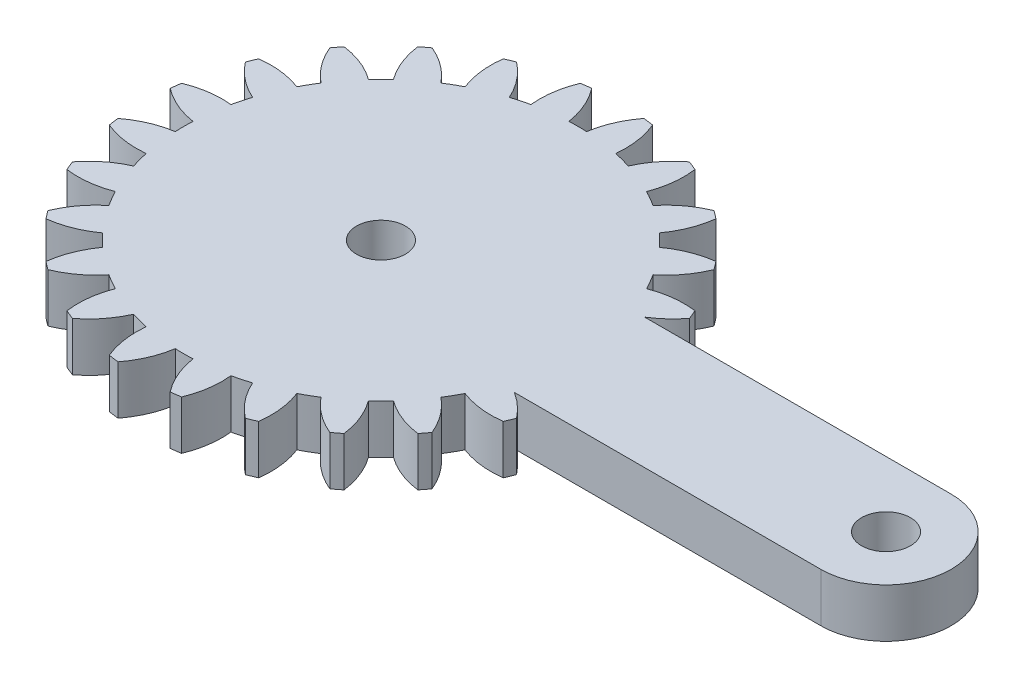
SolidWorks part; units mm, degrees
ref_plane "Front Plane" through (0, 0, 0) normal (0, 0, 1) x (1, 0, 0)
ref_plane "Top Plane" through (0, 0, 0) normal (0, 1, 0) x (1, 0, 0)
ref_plane "Right Plane" through (0, 0, 0) normal (1, 0, 0) x (0, 0, -1)
sketch "Sketch1" plane through (0, 0, 0) normal (0, 1, 0) x (1, 0, 0)
  line L0 (20.8937, 4) -> (2.0816, 4)
  line L1 (2.0816, -4) -> (20.8937, -4)
  line L2 (20.8937, 0) -> (-10.1063, 0) construction
  arc A0 (2.0816, 4) -> (3.5217, 5.3071) centre (-0.7683, 8.5867) ccw
  arc A1 (3.5217, 5.3071) -> (3.2829, 5.8838) centre (-10.1063, 0) ccw
  arc A2 (3.2829, 5.8838) -> (0.6271, 5.5703) centre (2.5684, 0.5313) ccw
  arc A3 (0.6271, 5.5703) -> (0.0844, 6.5103) centre (-10.1063, 0) ccw
  arc A4 (0.0844, 6.5103) -> (1.6838, 8.6535) centre (-3.3089, 10.711) ccw
  arc A5 (1.6838, 8.6535) -> (1.3038, 9.1487) centre (-10.1063, 0) ccw
  arc A6 (1.3038, 9.1487) -> (-1.1803, 8.1585) centre (1.999, 3.7936) ccw
  arc A7 (-1.1803, 8.1585) -> (-1.9479, 8.926) centre (-10.1063, 0) ccw
  arc A8 (-1.9479, 8.926) -> (-0.9576, 11.4102) centre (-6.3127, 12.1053) ccw
  arc A9 (-0.9576, 11.4102) -> (-1.4528, 11.7901) centre (-10.1063, 0) ccw
  arc A10 (-1.4528, 11.7901) -> (-3.596, 10.1907) centre (0.6046, 6.7975) ccw
  arc A11 (-3.596, 10.1907) -> (-4.5361, 10.7334) centre (-10.1063, 0) ccw
  arc A12 (-4.5361, 10.7334) -> (-4.2225, 13.3892) centre (-9.5751, 12.6747) ccw
  arc A13 (-4.2225, 13.3892) -> (-4.7992, 13.6281) centre (-10.1063, 0) ccw
  arc A14 (-4.7992, 13.6281) -> (-6.4554, 11.5285) centre (-1.5196, 9.3381) ccw
  arc A15 (-6.4554, 11.5285) -> (-7.5039, 11.8094) centre (-10.1063, 0) ccw
  arc A16 (-7.5039, 11.8094) -> (-7.8884, 14.4558) centre (-12.8736, 12.3803) ccw
  arc A17 (-7.8884, 14.4558) -> (-8.5072, 14.5373) centre (-10.1063, 0) ccw
  arc A18 (-8.5072, 14.5373) -> (-9.5636, 12.0806) centre (-4.2291, 11.2423) ccw
  arc A19 (-9.5636, 12.0806) -> (-10.6491, 12.0806) centre (-10.1063, 0) ccw
  arc A20 (-10.6491, 12.0806) -> (-11.7054, 14.5373) centre (-15.9836, 11.2423) ccw
  arc A21 (-11.7054, 14.5373) -> (-12.3243, 14.4558) centre (-10.1063, 0) ccw
  arc A22 (-12.3243, 14.4558) -> (-12.7088, 11.8094) centre (-7.3391, 12.3803) ccw
  arc A23 (-12.7088, 11.8094) -> (-13.7573, 11.5285) centre (-10.1063, 0) ccw
  arc A24 (-13.7573, 11.5285) -> (-15.4135, 13.6281) centre (-18.6931, 9.3381) ccw
  arc A25 (-15.4135, 13.6281) -> (-15.9901, 13.3892) centre (-10.1063, 0) ccw
  arc A26 (-15.9901, 13.3892) -> (-15.6766, 10.7334) centre (-10.6376, 12.6747) ccw
  arc A27 (-15.6766, 10.7334) -> (-16.6166, 10.1907) centre (-10.1063, 0) ccw
  arc A28 (-16.6166, 10.1907) -> (-18.7599, 11.7901) centre (-20.8173, 6.7975) ccw
  arc A29 (-18.7599, 11.7901) -> (-19.255, 11.4102) centre (-10.1063, 0) ccw
  arc A30 (-19.255, 11.4102) -> (-18.2648, 8.926) centre (-13.9, 12.1053) ccw
  arc A31 (-18.2648, 8.926) -> (-19.0324, 8.1585) centre (-10.1063, 0) ccw
  arc A32 (-19.0324, 8.1585) -> (-21.5165, 9.1487) centre (-22.2117, 3.7936) ccw
  arc A33 (-21.5165, 9.1487) -> (-21.8965, 8.6535) centre (-10.1063, 0) ccw
  arc A34 (-21.8965, 8.6535) -> (-20.2971, 6.5103) centre (-16.9038, 10.711) ccw
  arc A35 (-20.2971, 6.5103) -> (-20.8398, 5.5703) centre (-10.1063, 0) ccw
  arc A36 (-20.8398, 5.5703) -> (-23.4956, 5.8838) centre (-22.7811, 0.5313) ccw
  arc A37 (-23.4956, 5.8838) -> (-23.7344, 5.3071) centre (-10.1063, 0) ccw
  arc A38 (-23.7344, 5.3071) -> (-21.6348, 3.6509) centre (-19.4444, 8.5867) ccw
  arc A39 (-21.6348, 3.6509) -> (-21.9157, 2.6025) centre (-10.1063, 0) ccw
  arc A40 (-21.9157, 2.6025) -> (-24.5622, 2.2179) centre (-22.4867, -2.7673) ccw
  arc A41 (-24.5622, 2.2179) -> (-24.6437, 1.5991) centre (-10.1063, 0) ccw
  arc A42 (-24.6437, 1.5991) -> (-22.1869, 0.5427) centre (-21.3486, 5.8773) ccw
  arc A43 (-22.1869, 0.5427) -> (-22.1869, -0.5427) centre (-10.1063, 0) ccw
  arc A44 (-22.1869, -0.5427) -> (-24.6437, -1.5991) centre (-21.3486, -5.8773) ccw
  arc A45 (-24.6437, -1.5991) -> (-24.5622, -2.2179) centre (-10.1063, 0) ccw
  arc A46 (-24.5622, -2.2179) -> (-21.9157, -2.6025) centre (-22.4867, 2.7673) ccw
  arc A47 (-21.9157, -2.6025) -> (-21.6348, -3.6509) centre (-10.1063, 0) ccw
  arc A48 (-21.6348, -3.6509) -> (-23.7344, -5.3071) centre (-19.4444, -8.5867) ccw
  arc A49 (-23.7344, -5.3071) -> (-23.4956, -5.8838) centre (-10.1063, 0) ccw
  arc A50 (-23.4956, -5.8838) -> (-20.8398, -5.5703) centre (-22.7811, -0.5313) ccw
  arc A51 (-20.8398, -5.5703) -> (-20.2971, -6.5103) centre (-10.1063, 0) ccw
  arc A52 (-20.2971, -6.5103) -> (-21.8965, -8.6535) centre (-16.9038, -10.711) ccw
  arc A53 (-21.8965, -8.6535) -> (-21.5165, -9.1487) centre (-10.1063, 0) ccw
  arc A54 (-21.5165, -9.1487) -> (-19.0324, -8.1585) centre (-22.2117, -3.7936) ccw
  arc A55 (-19.0324, -8.1585) -> (-18.2648, -8.926) centre (-10.1063, 0) ccw
  arc A56 (-18.2648, -8.926) -> (-19.255, -11.4102) centre (-13.9, -12.1053) ccw
  arc A57 (-19.255, -11.4102) -> (-18.7599, -11.7901) centre (-10.1063, 0) ccw
  arc A58 (-18.7599, -11.7901) -> (-16.6166, -10.1907) centre (-20.8173, -6.7975) ccw
  arc A59 (-16.6166, -10.1907) -> (-15.6766, -10.7334) centre (-10.1063, 0) ccw
  arc A60 (-15.6766, -10.7334) -> (-15.9901, -13.3892) centre (-10.6376, -12.6747) ccw
  arc A61 (-15.9901, -13.3892) -> (-15.4135, -13.6281) centre (-10.1063, 0) ccw
  arc A62 (-15.4135, -13.6281) -> (-13.7573, -11.5285) centre (-18.6931, -9.3381) ccw
  arc A63 (-13.7573, -11.5285) -> (-12.7088, -11.8094) centre (-10.1063, 0) ccw
  arc A64 (-12.7088, -11.8094) -> (-12.3243, -14.4558) centre (-7.3391, -12.3803) ccw
  arc A65 (-12.3243, -14.4558) -> (-11.7054, -14.5373) centre (-10.1063, 0) ccw
  arc A66 (-11.7054, -14.5373) -> (-10.6491, -12.0806) centre (-15.9836, -11.2423) ccw
  arc A67 (-10.6491, -12.0806) -> (-9.5636, -12.0806) centre (-10.1063, 0) ccw
  arc A68 (-9.5636, -12.0806) -> (-8.5072, -14.5373) centre (-4.2291, -11.2423) ccw
  arc A69 (-8.5072, -14.5373) -> (-7.8884, -14.4558) centre (-10.1063, 0) ccw
  arc A70 (-7.8884, -14.4558) -> (-7.5039, -11.8094) centre (-12.8736, -12.3803) ccw
  arc A71 (-7.5039, -11.8094) -> (-6.4554, -11.5285) centre (-10.1063, 0) ccw
  arc A72 (-6.4554, -11.5285) -> (-4.7992, -13.6281) centre (-1.5196, -9.3381) ccw
  arc A73 (-4.7992, -13.6281) -> (-4.2225, -13.3892) centre (-10.1063, 0) ccw
  arc A74 (-4.2225, -13.3892) -> (-4.5361, -10.7334) centre (-9.5751, -12.6747) ccw
  arc A75 (-4.5361, -10.7334) -> (-3.596, -10.1907) centre (-10.1063, 0) ccw
  arc A76 (-3.596, -10.1907) -> (-1.4528, -11.7901) centre (0.6046, -6.7975) ccw
  arc A77 (-1.4528, -11.7901) -> (-0.9576, -11.4102) centre (-10.1063, 0) ccw
  arc A78 (-0.9576, -11.4102) -> (-1.9479, -8.926) centre (-6.3127, -12.1053) ccw
  arc A79 (-1.9479, -8.926) -> (-1.1803, -8.1585) centre (-10.1063, 0) ccw
  arc A80 (-1.1803, -8.1585) -> (1.3038, -9.1487) centre (1.999, -3.7936) ccw
  arc A81 (1.3038, -9.1487) -> (1.6838, -8.6535) centre (-10.1063, 0) ccw
  arc A82 (1.6838, -8.6535) -> (0.0844, -6.5103) centre (-3.3089, -10.711) ccw
  arc A83 (0.0844, -6.5103) -> (0.6271, -5.5703) centre (-10.1063, 0) ccw
  arc A84 (0.6271, -5.5703) -> (3.2829, -5.8838) centre (2.5684, -0.5313) ccw
  arc A85 (3.2829, -5.8838) -> (3.5217, -5.3071) centre (-10.1063, 0) ccw
  arc A86 (3.5217, -5.3071) -> (2.0816, -4) centre (-0.7683, -8.5867) ccw
  arc A87 (20.8937, -4) -> (20.8937, 4) centre (20.8937, 0) ccw
  circle A88 centre (-10.1063, 0) radius 1.5
  circle A89 centre (20.8937, 0) radius 1.5
  dimension "D1" = 3
  dimension "D2" = 3
  dimension "D3" = 31
extrude "Boss-Extrude1" add sketch "Sketch1" along normal blind 3
sketch "Sketch2" plane through (0, 3, 0) normal (0, 1, 0) x (1, 0, 0)
  line L0 (2.0816, -4) -> (1.3057, -4)
  line L1 (20.8937, 0) -> (-10.1063, 0) construction
  line L2 (20.8937, 4) -> (2.0816, 4)
  line L3 (2.0816, -4) -> (20.8937, -4)
  line L4 (20.8937, 4) -> (2.0816, 4)
  line L5 (2.0816, -4) -> (20.8937, -4)
  circle A0 centre (-10.1063, 0) radius 12.0927
  arc A88 (20.8937, -4) -> (20.8937, 4) centre (20.8937, 0) ccw
  arc A89 (2.0816, 4) -> (3.5217, 5.3071) centre (-0.7683, 8.5867) ccw
  arc A90 (3.5217, 5.3071) -> (3.2829, 5.8838) centre (-10.1063, 0) ccw
  arc A91 (3.2829, 5.8838) -> (0.6271, 5.5703) centre (2.5684, 0.5313) ccw
  arc A92 (0.6271, 5.5703) -> (0.0844, 6.5103) centre (-10.1063, 0) ccw
  arc A93 (0.0844, 6.5103) -> (1.6838, 8.6535) centre (-3.3089, 10.711) ccw
  arc A94 (1.6838, 8.6535) -> (1.3038, 9.1487) centre (-10.1063, 0) ccw
  arc A95 (1.3038, 9.1487) -> (-1.1803, 8.1585) centre (1.999, 3.7936) ccw
  arc A96 (-1.1803, 8.1585) -> (-1.9479, 8.926) centre (-10.1063, 0) ccw
  arc A97 (-1.9479, 8.926) -> (-0.9576, 11.4102) centre (-6.3127, 12.1053) ccw
  arc A98 (-0.9576, 11.4102) -> (-1.4528, 11.7901) centre (-10.1063, 0) ccw
  arc A99 (-1.4528, 11.7901) -> (-3.596, 10.1907) centre (0.6046, 6.7975) ccw
  arc A100 (-3.596, 10.1907) -> (-4.5361, 10.7334) centre (-10.1063, 0) ccw
  arc A101 (-4.5361, 10.7334) -> (-4.2225, 13.3892) centre (-9.5751, 12.6747) ccw
  arc A102 (-4.2225, 13.3892) -> (-4.7992, 13.6281) centre (-10.1063, 0) ccw
  arc A103 (-4.7992, 13.6281) -> (-6.4554, 11.5285) centre (-1.5196, 9.3381) ccw
  arc A104 (-6.4554, 11.5285) -> (-7.5039, 11.8094) centre (-10.1063, 0) ccw
  arc A105 (-7.5039, 11.8094) -> (-7.8884, 14.4558) centre (-12.8736, 12.3803) ccw
  arc A106 (-7.8884, 14.4558) -> (-8.5072, 14.5373) centre (-10.1063, 0) ccw
  arc A107 (-8.5072, 14.5373) -> (-9.5636, 12.0806) centre (-4.2291, 11.2423) ccw
  arc A108 (-9.5636, 12.0806) -> (-10.6491, 12.0806) centre (-10.1063, 0) ccw
  arc A109 (-10.6491, 12.0806) -> (-11.7054, 14.5373) centre (-15.9836, 11.2423) ccw
  arc A110 (-11.7054, 14.5373) -> (-12.3243, 14.4558) centre (-10.1063, 0) ccw
  arc A111 (-12.3243, 14.4558) -> (-12.7088, 11.8094) centre (-7.3391, 12.3803) ccw
  arc A112 (-12.7088, 11.8094) -> (-13.7573, 11.5285) centre (-10.1063, 0) ccw
  arc A113 (-13.7573, 11.5285) -> (-15.4135, 13.6281) centre (-18.6931, 9.3381) ccw
  arc A114 (-15.4135, 13.6281) -> (-15.9901, 13.3892) centre (-10.1063, 0) ccw
  arc A115 (-15.9901, 13.3892) -> (-15.6766, 10.7334) centre (-10.6376, 12.6747) ccw
  arc A116 (-15.6766, 10.7334) -> (-16.6166, 10.1907) centre (-10.1063, 0) ccw
  arc A117 (-16.6166, 10.1907) -> (-18.7599, 11.7901) centre (-20.8173, 6.7975) ccw
  arc A118 (-18.7599, 11.7901) -> (-19.255, 11.4102) centre (-10.1063, 0) ccw
  arc A119 (-19.255, 11.4102) -> (-18.2648, 8.926) centre (-13.9, 12.1053) ccw
  arc A120 (-18.2648, 8.926) -> (-19.0324, 8.1585) centre (-10.1063, 0) ccw
  arc A121 (-19.0324, 8.1585) -> (-21.5165, 9.1487) centre (-22.2117, 3.7936) ccw
  arc A122 (-21.5165, 9.1487) -> (-21.8965, 8.6535) centre (-10.1063, 0) ccw
  arc A123 (-21.8965, 8.6535) -> (-20.2971, 6.5103) centre (-16.9038, 10.711) ccw
  arc A124 (-20.2971, 6.5103) -> (-20.8398, 5.5703) centre (-10.1063, 0) ccw
  arc A125 (-20.8398, 5.5703) -> (-23.4956, 5.8838) centre (-22.7811, 0.5313) ccw
  arc A126 (-23.4956, 5.8838) -> (-23.7344, 5.3071) centre (-10.1063, 0) ccw
  arc A127 (-23.7344, 5.3071) -> (-21.6348, 3.6509) centre (-19.4444, 8.5867) ccw
  arc A128 (-21.6348, 3.6509) -> (-21.9157, 2.6025) centre (-10.1063, 0) ccw
  arc A129 (-21.9157, 2.6025) -> (-24.5622, 2.2179) centre (-22.4867, -2.7673) ccw
  arc A130 (-24.5622, 2.2179) -> (-24.6437, 1.5991) centre (-10.1063, 0) ccw
  arc A131 (-24.6437, 1.5991) -> (-22.1869, 0.5427) centre (-21.3486, 5.8773) ccw
  arc A132 (-22.1869, 0.5427) -> (-22.1869, -0.5427) centre (-10.1063, 0) ccw
  arc A133 (-22.1869, -0.5427) -> (-24.6437, -1.5991) centre (-21.3486, -5.8773) ccw
  arc A134 (-24.6437, -1.5991) -> (-24.5622, -2.2179) centre (-10.1063, 0) ccw
  arc A135 (-24.5622, -2.2179) -> (-21.9157, -2.6025) centre (-22.4867, 2.7673) ccw
  arc A136 (-21.9157, -2.6025) -> (-21.6348, -3.6509) centre (-10.1063, 0) ccw
  arc A137 (-21.6348, -3.6509) -> (-23.7344, -5.3071) centre (-19.4444, -8.5867) ccw
  arc A138 (-23.7344, -5.3071) -> (-23.4956, -5.8838) centre (-10.1063, 0) ccw
  arc A139 (-23.4956, -5.8838) -> (-20.8398, -5.5703) centre (-22.7811, -0.5313) ccw
  arc A140 (-20.8398, -5.5703) -> (-20.2971, -6.5103) centre (-10.1063, 0) ccw
  arc A141 (-20.2971, -6.5103) -> (-21.8965, -8.6535) centre (-16.9038, -10.711) ccw
  arc A142 (-21.8965, -8.6535) -> (-21.5165, -9.1487) centre (-10.1063, 0) ccw
  arc A143 (-21.5165, -9.1487) -> (-19.0324, -8.1585) centre (-22.2117, -3.7936) ccw
  arc A144 (-19.0324, -8.1585) -> (-18.2648, -8.926) centre (-10.1063, 0) ccw
  arc A145 (-18.2648, -8.926) -> (-19.255, -11.4102) centre (-13.9, -12.1053) ccw
  arc A146 (-19.255, -11.4102) -> (-18.7599, -11.7901) centre (-10.1063, 0) ccw
  arc A147 (-18.7599, -11.7901) -> (-16.6166, -10.1907) centre (-20.8173, -6.7975) ccw
  arc A148 (-16.6166, -10.1907) -> (-15.6766, -10.7334) centre (-10.1063, 0) ccw
  arc A149 (-15.6766, -10.7334) -> (-15.9901, -13.3892) centre (-10.6376, -12.6747) ccw
  arc A150 (-15.9901, -13.3892) -> (-15.4135, -13.6281) centre (-10.1063, 0) ccw
  arc A151 (-15.4135, -13.6281) -> (-13.7573, -11.5285) centre (-18.6931, -9.3381) ccw
  arc A152 (-13.7573, -11.5285) -> (-12.7088, -11.8094) centre (-10.1063, 0) ccw
  arc A153 (-12.7088, -11.8094) -> (-12.3243, -14.4558) centre (-7.3391, -12.3803) ccw
  arc A154 (-12.3243, -14.4558) -> (-11.7054, -14.5373) centre (-10.1063, 0) ccw
  arc A155 (-11.7054, -14.5373) -> (-10.6491, -12.0806) centre (-15.9836, -11.2423) ccw
  arc A156 (-10.6491, -12.0806) -> (-9.5636, -12.0806) centre (-10.1063, 0) ccw
  arc A157 (-9.5636, -12.0806) -> (-8.5072, -14.5373) centre (-4.2291, -11.2423) ccw
  arc A158 (-8.5072, -14.5373) -> (-7.8884, -14.4558) centre (-10.1063, 0) ccw
  arc A159 (-7.8884, -14.4558) -> (-7.5039, -11.8094) centre (-12.8736, -12.3803) ccw
  arc A160 (-7.5039, -11.8094) -> (-6.4554, -11.5285) centre (-10.1063, 0) ccw
  arc A161 (-6.4554, -11.5285) -> (-4.7992, -13.6281) centre (-1.5196, -9.3381) ccw
  arc A162 (-4.7992, -13.6281) -> (-4.2225, -13.3892) centre (-10.1063, 0) ccw
  arc A163 (-4.2225, -13.3892) -> (-4.5361, -10.7334) centre (-9.5751, -12.6747) ccw
  arc A164 (-4.5361, -10.7334) -> (-3.596, -10.1907) centre (-10.1063, 0) ccw
  arc A165 (-3.596, -10.1907) -> (-1.4528, -11.7901) centre (0.6046, -6.7975) ccw
  arc A166 (-1.4528, -11.7901) -> (-0.9576, -11.4102) centre (-10.1063, 0) ccw
  arc A167 (-0.9576, -11.4102) -> (-1.9479, -8.926) centre (-6.3127, -12.1053) ccw
  arc A168 (-1.9479, -8.926) -> (-1.1803, -8.1585) centre (-10.1063, 0) ccw
  arc A169 (-1.1803, -8.1585) -> (1.3038, -9.1487) centre (1.999, -3.7936) ccw
  arc A170 (1.3038, -9.1487) -> (1.6838, -8.6535) centre (-10.1063, 0) ccw
  arc A171 (1.6838, -8.6535) -> (0.0844, -6.5103) centre (-3.3089, -10.711) ccw
  arc A172 (0.0844, -6.5103) -> (0.6271, -5.5703) centre (-10.1063, 0) ccw
  arc A173 (0.6271, -5.5703) -> (3.2829, -5.8838) centre (2.5684, -0.5313) ccw
  arc A174 (3.2829, -5.8838) -> (3.5217, -5.3071) centre (-10.1063, 0) ccw
  arc A175 (3.5217, -5.3071) -> (2.0816, -4) centre (-0.7683, -8.5867) ccw
  arc A176 (20.8937, -4) -> (20.8937, 4) centre (20.8937, 0) ccw
  arc A177 (2.0816, 4) -> (3.5217, 5.3071) centre (-0.7683, 8.5867) ccw
  arc A178 (3.5217, 5.3071) -> (3.2829, 5.8838) centre (-10.1063, 0) ccw
  arc A179 (3.2829, 5.8838) -> (0.6271, 5.5703) centre (2.5684, 0.5313) ccw
  arc A180 (0.6271, 5.5703) -> (0.0844, 6.5103) centre (-10.1063, 0) ccw
  arc A181 (0.0844, 6.5103) -> (1.6838, 8.6535) centre (-3.3089, 10.711) ccw
  arc A182 (1.6838, 8.6535) -> (1.3038, 9.1487) centre (-10.1063, 0) ccw
  arc A183 (1.3038, 9.1487) -> (-1.1803, 8.1585) centre (1.999, 3.7936) ccw
  arc A184 (-1.1803, 8.1585) -> (-1.9479, 8.926) centre (-10.1063, 0) ccw
  arc A185 (-1.9479, 8.926) -> (-0.9576, 11.4102) centre (-6.3127, 12.1053) ccw
  arc A186 (-0.9576, 11.4102) -> (-1.4528, 11.7901) centre (-10.1063, 0) ccw
  arc A187 (-1.4528, 11.7901) -> (-3.596, 10.1907) centre (0.6046, 6.7975) ccw
  arc A188 (-3.596, 10.1907) -> (-4.5361, 10.7334) centre (-10.1063, 0) ccw
  arc A189 (-4.5361, 10.7334) -> (-4.2225, 13.3892) centre (-9.5751, 12.6747) ccw
  arc A190 (-4.2225, 13.3892) -> (-4.7992, 13.6281) centre (-10.1063, 0) ccw
  arc A191 (-4.7992, 13.6281) -> (-6.4554, 11.5285) centre (-1.5196, 9.3381) ccw
  arc A192 (-6.4554, 11.5285) -> (-7.5039, 11.8094) centre (-10.1063, 0) ccw
  arc A193 (-7.5039, 11.8094) -> (-7.8884, 14.4558) centre (-12.8736, 12.3803) ccw
  arc A194 (-7.8884, 14.4558) -> (-8.5072, 14.5373) centre (-10.1063, 0) ccw
  arc A195 (-8.5072, 14.5373) -> (-9.5636, 12.0806) centre (-4.2291, 11.2423) ccw
  arc A196 (-9.5636, 12.0806) -> (-10.6491, 12.0806) centre (-10.1063, 0) ccw
  arc A197 (-10.6491, 12.0806) -> (-11.7054, 14.5373) centre (-15.9836, 11.2423) ccw
  arc A198 (-11.7054, 14.5373) -> (-12.3243, 14.4558) centre (-10.1063, 0) ccw
  arc A199 (-12.3243, 14.4558) -> (-12.7088, 11.8094) centre (-7.3391, 12.3803) ccw
  arc A200 (-12.7088, 11.8094) -> (-13.7573, 11.5285) centre (-10.1063, 0) ccw
  arc A201 (-13.7573, 11.5285) -> (-15.4135, 13.6281) centre (-18.6931, 9.3381) ccw
  arc A202 (-15.4135, 13.6281) -> (-15.9901, 13.3892) centre (-10.1063, 0) ccw
  arc A203 (-15.9901, 13.3892) -> (-15.6766, 10.7334) centre (-10.6376, 12.6747) ccw
  arc A204 (-15.6766, 10.7334) -> (-16.6166, 10.1907) centre (-10.1063, 0) ccw
  arc A205 (-16.6166, 10.1907) -> (-18.7599, 11.7901) centre (-20.8173, 6.7975) ccw
  arc A206 (-18.7599, 11.7901) -> (-19.255, 11.4102) centre (-10.1063, 0) ccw
  arc A207 (-19.255, 11.4102) -> (-18.2648, 8.926) centre (-13.9, 12.1053) ccw
  arc A208 (-18.2648, 8.926) -> (-19.0324, 8.1585) centre (-10.1063, 0) ccw
  arc A209 (-19.0324, 8.1585) -> (-21.5165, 9.1487) centre (-22.2117, 3.7936) ccw
  arc A210 (-21.5165, 9.1487) -> (-21.8965, 8.6535) centre (-10.1063, 0) ccw
  arc A211 (-21.8965, 8.6535) -> (-20.2971, 6.5103) centre (-16.9038, 10.711) ccw
  arc A212 (-20.2971, 6.5103) -> (-20.8398, 5.5703) centre (-10.1063, 0) ccw
  arc A213 (-20.8398, 5.5703) -> (-23.4956, 5.8838) centre (-22.7811, 0.5313) ccw
  arc A214 (-23.4956, 5.8838) -> (-23.7344, 5.3071) centre (-10.1063, 0) ccw
  arc A215 (-23.7344, 5.3071) -> (-21.6348, 3.6509) centre (-19.4444, 8.5867) ccw
  arc A216 (-21.6348, 3.6509) -> (-21.9157, 2.6025) centre (-10.1063, 0) ccw
  arc A217 (-21.9157, 2.6025) -> (-24.5622, 2.2179) centre (-22.4867, -2.7673) ccw
  arc A218 (-24.5622, 2.2179) -> (-24.6437, 1.5991) centre (-10.1063, 0) ccw
  arc A219 (-24.6437, 1.5991) -> (-22.1869, 0.5427) centre (-21.3486, 5.8773) ccw
  arc A220 (-22.1869, 0.5427) -> (-22.1869, -0.5427) centre (-10.1063, 0) ccw
  arc A221 (-22.1869, -0.5427) -> (-24.6437, -1.5991) centre (-21.3486, -5.8773) ccw
  arc A222 (-24.6437, -1.5991) -> (-24.5622, -2.2179) centre (-10.1063, 0) ccw
  arc A223 (-24.5622, -2.2179) -> (-21.9157, -2.6025) centre (-22.4867, 2.7673) ccw
  arc A224 (-21.9157, -2.6025) -> (-21.6348, -3.6509) centre (-10.1063, 0) ccw
  arc A225 (-21.6348, -3.6509) -> (-23.7344, -5.3071) centre (-19.4444, -8.5867) ccw
  arc A226 (-23.7344, -5.3071) -> (-23.4956, -5.8838) centre (-10.1063, 0) ccw
  arc A227 (-23.4956, -5.8838) -> (-20.8398, -5.5703) centre (-22.7811, -0.5313) ccw
  arc A228 (-20.8398, -5.5703) -> (-20.2971, -6.5103) centre (-10.1063, 0) ccw
  arc A229 (-20.2971, -6.5103) -> (-21.8965, -8.6535) centre (-16.9038, -10.711) ccw
  arc A230 (-21.8965, -8.6535) -> (-21.5165, -9.1487) centre (-10.1063, 0) ccw
  arc A231 (-21.5165, -9.1487) -> (-19.0324, -8.1585) centre (-22.2117, -3.7936) ccw
  arc A232 (-19.0324, -8.1585) -> (-18.2648, -8.926) centre (-10.1063, 0) ccw
  arc A233 (-18.2648, -8.926) -> (-19.255, -11.4102) centre (-13.9, -12.1053) ccw
  arc A234 (-19.255, -11.4102) -> (-18.7599, -11.7901) centre (-10.1063, 0) ccw
  arc A235 (-18.7599, -11.7901) -> (-16.6166, -10.1907) centre (-20.8173, -6.7975) ccw
  arc A236 (-16.6166, -10.1907) -> (-15.6766, -10.7334) centre (-10.1063, 0) ccw
  arc A237 (-15.6766, -10.7334) -> (-15.9901, -13.3892) centre (-10.6376, -12.6747) ccw
  arc A238 (-15.9901, -13.3892) -> (-15.4135, -13.6281) centre (-10.1063, 0) ccw
  arc A239 (-15.4135, -13.6281) -> (-13.7573, -11.5285) centre (-18.6931, -9.3381) ccw
  arc A240 (-13.7573, -11.5285) -> (-12.7088, -11.8094) centre (-10.1063, 0) ccw
  arc A241 (-12.7088, -11.8094) -> (-12.3243, -14.4558) centre (-7.3391, -12.3803) ccw
  arc A242 (-12.3243, -14.4558) -> (-11.7054, -14.5373) centre (-10.1063, 0) ccw
  arc A243 (-11.7054, -14.5373) -> (-10.6491, -12.0806) centre (-15.9836, -11.2423) ccw
  arc A244 (-10.6491, -12.0806) -> (-9.5636, -12.0806) centre (-10.1063, 0) ccw
  arc A245 (-9.5636, -12.0806) -> (-8.5072, -14.5373) centre (-4.2291, -11.2423) ccw
  arc A246 (-8.5072, -14.5373) -> (-7.8884, -14.4558) centre (-10.1063, 0) ccw
  arc A247 (-7.8884, -14.4558) -> (-7.5039, -11.8094) centre (-12.8736, -12.3803) ccw
  arc A248 (-7.5039, -11.8094) -> (-6.4554, -11.5285) centre (-10.1063, 0) ccw
  arc A249 (-6.4554, -11.5285) -> (-4.7992, -13.6281) centre (-1.5196, -9.3381) ccw
  arc A250 (-4.7992, -13.6281) -> (-4.2225, -13.3892) centre (-10.1063, 0) ccw
  arc A251 (-4.2225, -13.3892) -> (-4.5361, -10.7334) centre (-9.5751, -12.6747) ccw
  arc A252 (-4.5361, -10.7334) -> (-3.596, -10.1907) centre (-10.1063, 0) ccw
  arc A253 (-3.596, -10.1907) -> (-1.4528, -11.7901) centre (0.6046, -6.7975) ccw
  arc A254 (-1.4528, -11.7901) -> (-0.9576, -11.4102) centre (-10.1063, 0) ccw
  arc A255 (-0.9576, -11.4102) -> (-1.9479, -8.926) centre (-6.3127, -12.1053) ccw
  arc A256 (-1.9479, -8.926) -> (-1.1803, -8.1585) centre (-10.1063, 0) ccw
  arc A257 (-1.1803, -8.1585) -> (1.3038, -9.1487) centre (1.999, -3.7936) ccw
  arc A258 (1.3038, -9.1487) -> (1.6838, -8.6535) centre (-10.1063, 0) ccw
  arc A259 (1.6838, -8.6535) -> (0.0844, -6.5103) centre (-3.3089, -10.711) ccw
  arc A260 (0.0844, -6.5103) -> (0.6271, -5.5703) centre (-10.1063, 0) ccw
  arc A261 (0.6271, -5.5703) -> (3.2829, -5.8838) centre (2.5684, -0.5313) ccw
  arc A262 (3.2829, -5.8838) -> (3.5217, -5.3071) centre (-10.1063, 0) ccw
  arc A263 (3.5217, -5.3071) -> (2.0816, -4) centre (-0.7683, -8.5867) ccw
  dimension "D1" = 0
